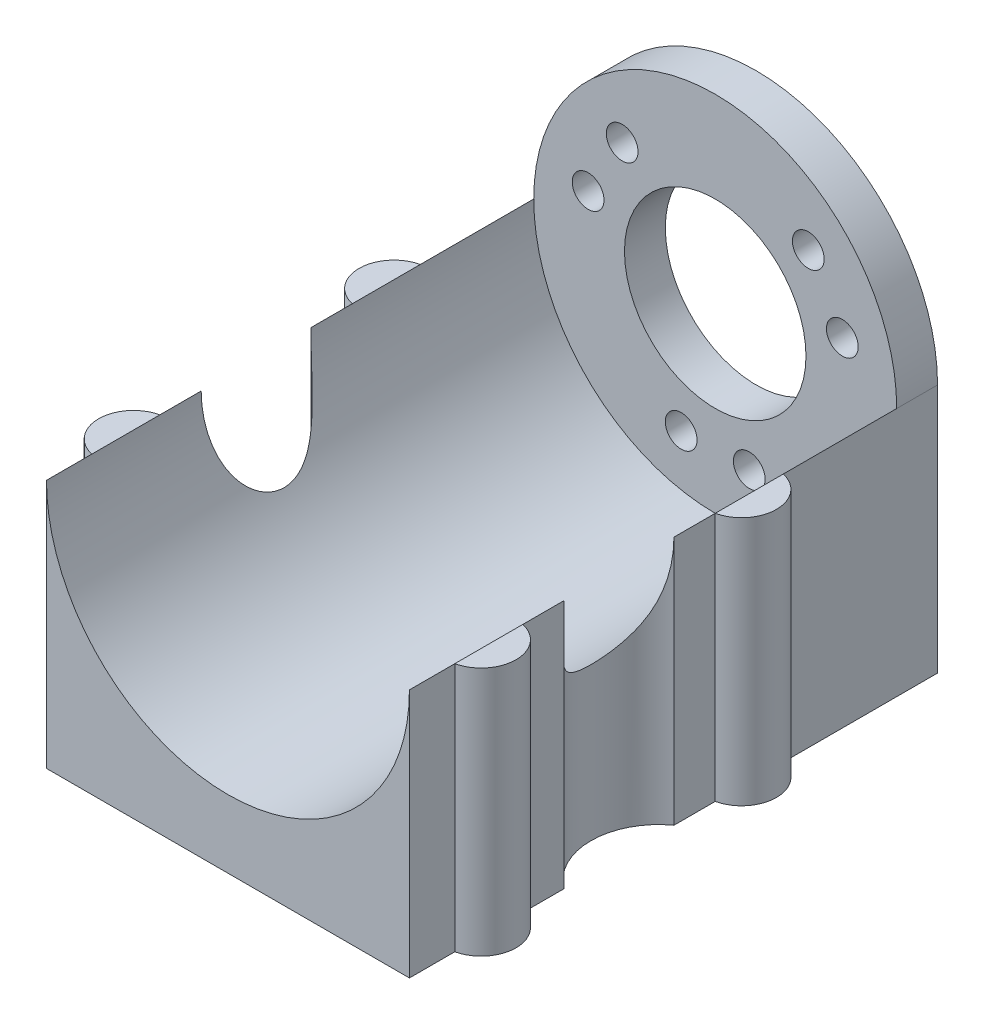
SolidWorks part; units mm, degrees
ref_plane "Front Plane" through (0, 0, 0) normal (0, 0, 1) x (1, 0, 0)
ref_plane "Top Plane" through (0, 0, 0) normal (0, 1, 0) x (1, 0, 0)
ref_plane "Right Plane" through (0, 0, 0) normal (1, 0, 0) x (0, 0, -1)
sketch "Sketch3" plane through (0, 0, 0) normal (0, 1, 0) x (1, 0, 0)
  line L0 (0, 0) -> (0, 53.7)
  line L1 (0, 53.7) -> (40, 53.7)
  line L2 (40, 53.7) -> (40, 0)
  line L3 (40, 0) -> (0, 0)
  dimension "D1" = 40
  dimension "D2" = 53.7
extrude "Boss-Extrude1" add sketch "Sketch3" along normal blind 27.5
sketch "Sketch4" plane through (0, 27.5, 0) normal (0, 1, 0) x (1, 0, 0)
  line L1 (0, 53.7) -> (0, 0) construction
  line L2 (0, 41.2) -> (0, 33.7)
  line L3 (0, 12.5) -> (0, 5)
  line L6 (40, 0) -> (40, 53.7) construction
  line L7 (40, 41.2) -> (40, 33.7)
  line L8 (40, 12.5) -> (40, 5)
  arc A4 (0, 33.7) -> (0, 41.2) centre (0.8438, 37.45) cw
  arc A5 (0, 5) -> (0, 12.5) centre (0.8438, 8.75) cw
  arc A7 (40, 33.7) -> (40, 41.2) centre (39.1562, 37.45) ccw
  arc A8 (40, 5) -> (40, 12.5) centre (39.1562, 8.75) ccw
  dimension "D3" = 12.5
  dimension "D6" = 5
  dimension "D8" = 0.8438
  dimension "D1" = 0.8438
  dimension "D4" = 0.8438
  dimension "D9" = 3.8438
  dimension "D12" = 3.8438
  dimension "D13" = 3.8438
  dimension "D2" = 0
  dimension "D5" = 7.5
  dimension "D7" = 0
  dimension "D10" = 0
  dimension "D11" = 12.5
  dimension "D14" = 0.8438
  dimension "D15" = 0
  dimension "D16" = 5
extrude "Boss-Extrude4" add sketch "Sketch4" against normal blind 27.5
sketch "Sketch6" plane through (0, 27.5, 0) normal (0, 1, 0) x (1, 0, 0)
  line L0 (0, 29.15) -> (0, 17.05)
  line L1 (0, 33.7) -> (0, 12.5) construction
  line L2 (40, 29.15) -> (40, 17.05)
  line L3 (40, 12.5) -> (40, 33.7) construction
  arc A0 (0, 17.05) -> (0, 29.15) centre (-4.3536, 23.1) ccw
  arc A2 (40, 17.05) -> (40, 29.15) centre (44.3536, 23.1) cw
  dimension "D2" = 7.4536
  dimension "D6" = 7.4536
  dimension "D1" = 12.1
  dimension "D3" = 0
  dimension "D4" = 4.55
  dimension "D5" = 12.1
  dimension "D7" = 0
  dimension "D8" = 4.55
extrude "Cut-Extrude1" cut sketch "Sketch6" against normal through all
sketch "Sketch7" plane through (0, 0, -53.7) normal (0, 0, -1) x (-1, 0, 0)
  line L1 (-40, 27.5) -> (0, 27.5) construction
  circle A2 centre (-20, 27.5) radius 20
  dimension "D1" = 40
extrude "Cut-Extrude2" cut sketch "Sketch7" against normal through all
sketch "Sketch8" plane through (0, 0, -53.7) normal (0, 0, -1) x (-1, 0, 0)
  line L4 (-40, 27.5) -> (-40, 0)
  line L5 (-40, 0) -> (0, 0)
  line L6 (0, 0) -> (0, 27.5)
  arc A1 (-40, 27.5) -> (0, 27.5) centre (-20, 27.5) cw
  dimension "D1" = 40
  dimension "D2" = 27.5
  dimension "D3" = 40
extrude "Boss-Extrude5" add sketch "Sketch8" along normal blind 4.5
sketch "Sketch9" plane through (0, 0, -58.2) normal (0, 0, -1) x (-1, 0, 0)
  circle A0 centre (-20, 27.5) radius 10
  dimension "D1" = 20
extrude "Cut-Extrude3" cut sketch "Sketch9" against normal through all
sketch "Sketch10" plane through (0, 0, -58.2) normal (0, 0, -1) x (-1, 0, 0)
  line L0 (-23.75, 13.4933) -> (-16.25, 13.4933) construction
  line L1 (-40, 0) -> (0, 0) construction
  line L2 (-30.2552, 37.7509) -> (-34.0052, 31.2558) construction
  line L3 (-20, 27.5) -> (9.0898, 44.295) construction
  line L4 (-20, 27.5) -> (-47.0626, 43.1246) construction
  line L5 (-5.9948, 31.2558) -> (-9.7448, 37.7509) construction
  line L7 (-20, 27.5) -> (-20, 3.387) construction
  circle A0 centre (-23.75, 13.4933) radius 1.75
  circle A1 centre (-16.25, 13.4933) radius 1.75
  circle A3 centre (-34.0052, 31.2558) radius 1.75
  circle A4 centre (-30.2552, 37.7509) radius 1.75
  circle A5 centre (-9.7448, 37.7509) radius 1.75
  circle A6 centre (-5.9948, 31.2558) radius 1.75
  point P10 (-32.1302, 34.5033)
  point P16 (-7.8698, 34.5033)
  dimension "D2" = 3.5
  dimension "D3" = 3.5
  dimension "D5" = 3.5
  dimension "D6" = 3.5
  dimension "D11" = 3.5
  dimension "D12" = 3.5
  dimension "D14" = 90
  dimension "D1" = 7.5
  dimension "D4" = 14.5
  dimension "D7" = 7.5
  dimension "D8" = 120
  dimension "D9" = 14.5
  dimension "D10" = 120
  dimension "D13" = 7.5
  dimension "D15" = 90
  dimension "D16" = 14.5
  dimension "D17" = 14.5
extrude "Cut-Extrude4" cut sketch "Sketch10" against normal through all
